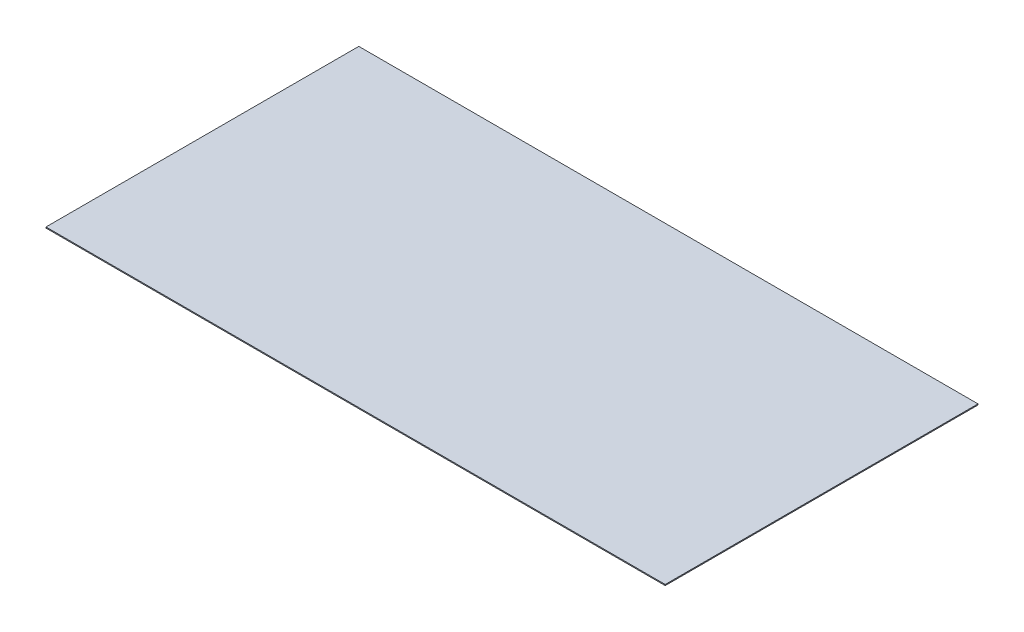
SolidWorks part; units mm, degrees
material "Glass"
ref_plane "Front Plane" through (0, 0, 0) normal (0, 0, 1) x (1, 0, 0)
ref_plane "Top Plane" through (0, 0, 0) normal (0, 1, 0) x (1, 0, 0)
ref_plane "Right Plane" through (0, 0, 0) normal (1, 0, 0) x (0, 0, -1)
sketch "Sketch1" plane through (0, 0, 0) normal (0, 1, 0) x (1, 0, 0)
  line L1 (-978, 494) -> (978, 494)
  line L2 (-978, 494) -> (-978, -494)
  line L3 (-978, -494) -> (978, -494)
  line L4 (978, 494) -> (978, -494)
  line L5 (-978, 494) -> (978, -494) construction
  line L6 (-978, -494) -> (978, 494) construction
  point P0 (0, 0)
  dimension "D1" = 1956
  dimension "D2" = 988
extrude "Boss-Extrude1" add sketch "Sketch1" along normal blind 3.2
